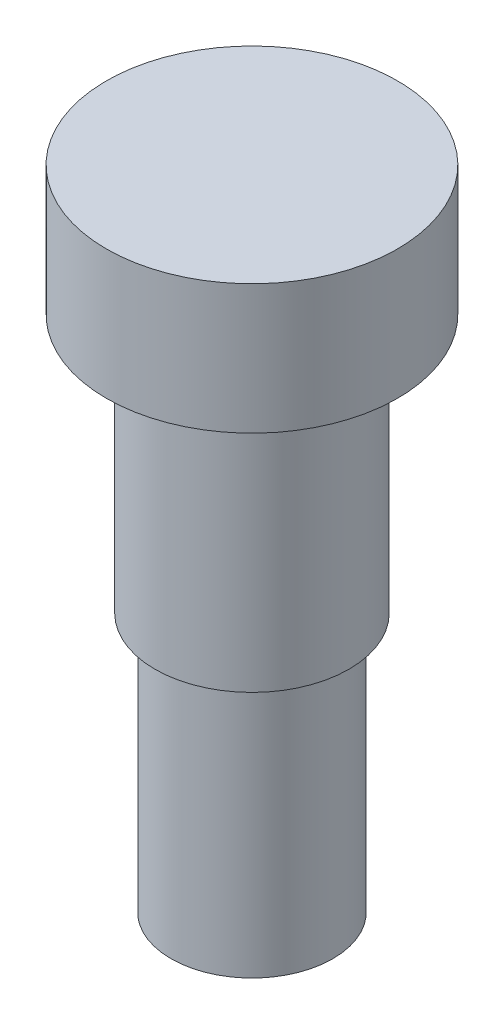
SolidWorks part; units mm, degrees
ref_plane "Front" through (0, 0, 0) normal (0, 0, 1) x (1, 0, 0)
ref_plane "Top" through (0, 0, 0) normal (0, 1, 0) x (1, 0, 0)
ref_plane "Right" through (0, 0, 0) normal (1, 0, 0) x (0, 0, -1)
sketch "profile" plane through (0, 0, 0) normal (0, 0, 1) x (1, 0, 0)
  line L0 (0, 24.8324) -> (0, -34.6109) construction
  line L1 (0, 6.35) -> (7.1438, 6.35)
  line L2 (7.1438, 6.35) -> (7.1438, 0)
  line L3 (7.1438, 0) -> (4.7625, 0)
  line L4 (4.7625, 0) -> (4.7625, -12.7)
  line L5 (4.7625, -12.7) -> (3.9688, -12.7)
  line L6 (3.9688, -12.7) -> (3.9688, -25.4)
  line L7 (3.9688, -25.4) -> (0, -25.4)
  line L8 (0, -25.4) -> (0, 6.35)
  dimension "head_diameter" = 14.2875
  dimension "shoulder_diameter" = 9.525
  dimension "thread_diameter" = 7.9375
  dimension "head_height" = 6.35
  dimension "shoulder_length" = 12.7
  dimension "thread_length" = 12.7
revolve "Base-Revolve" add sketch "profile" angle 360 about L0
